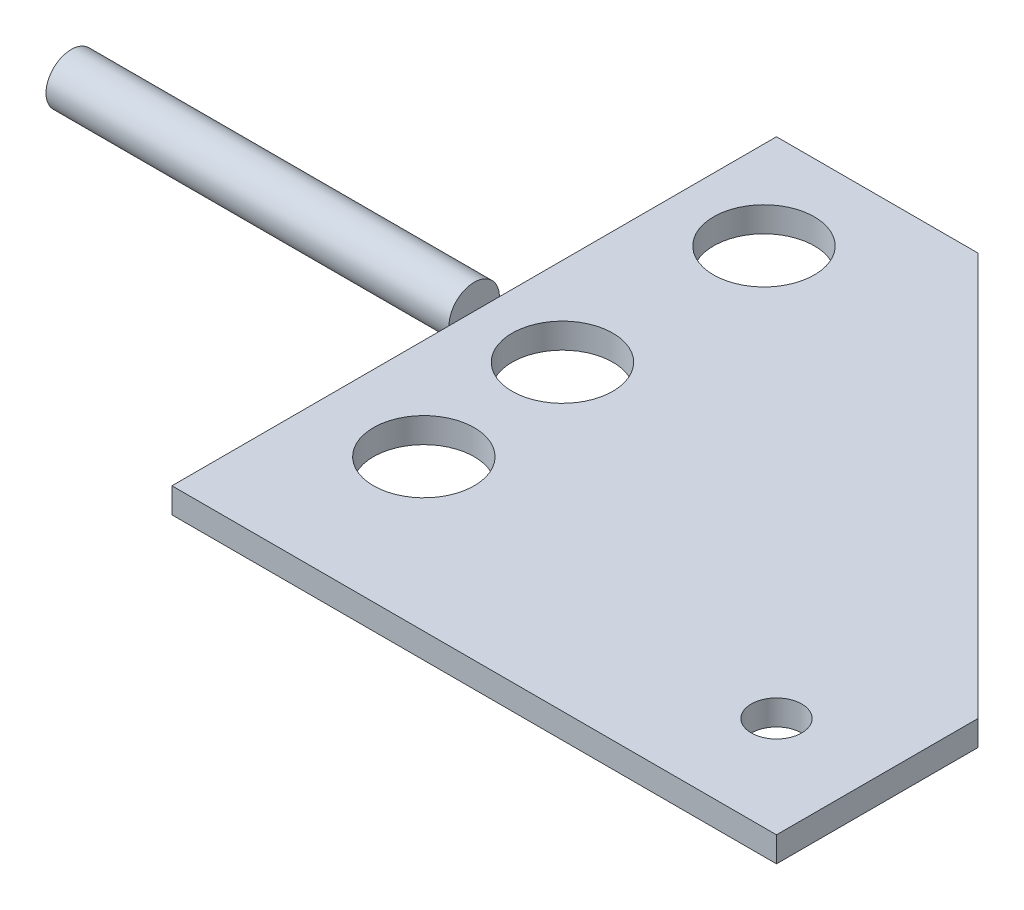
SolidWorks part; units mm, degrees
ref_plane "Front Plane" through (0, 0, 0) normal (0, 0, 1) x (1, 0, 0)
ref_plane "Top Plane" through (0, 0, 0) normal (0, 1, 0) x (1, 0, 0)
ref_plane "Right Plane" through (0, 0, 0) normal (1, 0, 0) x (0, 0, -1)
sketch "Sketch1" plane through (0, 0, 0) normal (0, 1, 0) x (1, 0, 0)
  line L0 (-76.2, 76.2) -> (-76.2, -76.2)
  line L1 (76.2, -76.2) -> (-76.2, -76.2) construction
  line L2 (76.2, -76.2) -> (76.2, 76.2) construction
  line L3 (76.2, 76.2) -> (-76.2, 76.2) construction
  line L4 (-76.2, -76.2) -> (-76.2, 76.2) construction
  line L5 (76.2, -76.2) -> (-76.2, 76.2) construction
  line L6 (76.2, 76.2) -> (-76.2, -76.2) construction
  line L7 (-76.2, -76.2) -> (76.2, -76.2)
  line L8 (76.2, -76.2) -> (76.2, -25.4)
  line L9 (76.2, -25.4) -> (-25.4, 76.2)
  line L10 (-25.4, 76.2) -> (-76.2, 76.2)
  point P0 (0, 0)
  dimension "D1" = 152.4
  dimension "D2" = 152.4
  dimension "D3" = 50.8
extrude "Boss-Extrude1" add sketch "Sketch1" along normal blind 6.35
sketch "Sketch2" plane through (-76.2, 0, 0) normal (-1, 0, 0) x (0, 0, 1)
  line L0 (-76.2, 6.35) -> (76.2, 6.35) construction
  circle A0 centre (0, 6.35) radius 6.35
  dimension "D1" = 12.7
extrude "Boss-Extrude2" add sketch "Sketch2" along normal blind 101.6
sketch "Sketch3" plane through (0, 6.35, 0) normal (0, 1, 0) x (1, 0, 0)
  line L1 (-76.2, -76.2) -> (-50.8, -76.2) construction
  line L2 (-76.2, -76.2) -> (-76.2, -38.1) construction
  line L3 (-76.2, -38.1) -> (-50.8, -38.1) construction
  line L4 (-50.8, -76.2) -> (-50.8, -38.1) construction
  line L5 (-76.2, -76.2) -> (-50.8, -38.1) construction
  line L6 (-76.2, -38.1) -> (-50.8, -76.2) construction
  line L7 (76.2, -76.2) -> (50.8, -76.2) construction
  line L8 (76.2, -76.2) -> (76.2, -50.8) construction
  line L9 (76.2, -50.8) -> (50.8, -50.8) construction
  line L10 (50.8, -76.2) -> (50.8, -50.8) construction
  line L11 (76.2, -76.2) -> (50.8, -50.8) construction
  line L12 (76.2, -50.8) -> (50.8, -76.2) construction
  circle A0 centre (-50.8, -38.1) radius 12.7
  circle A1 centre (50.8, -50.8) radius 6.35
  point P4 (-63.5, -57.15)
  point P11 (63.5, -63.5)
  dimension "D3" = 25.4
  dimension "D6" = 12.7
  dimension "D1" = 38.1
  dimension "D2" = 25.4
  dimension "D4" = 25.4
  dimension "D5" = 25.4
extrude "Cut-Extrude1" cut sketch "Sketch3" against normal blind 101.6
sketch "Sketch4" plane through (0, 6.35, 0) normal (0, 1, 0) x (1, 0, 0)
  line L0 (0, 0) -> (-53.9562, 0) construction
  circle A0 centre (-53.9562, 0) radius 12.7
  dimension "D1" = 25.4
extrude "Cut-Extrude2" cut sketch "Sketch4" against normal through all
sketch "Sketch5" plane through (0, 6.35, 0) normal (0, 1, 0) x (1, 0, 0)
  line L0 (-53.9562, 0) -> (-53.9562, 50.8) construction
  circle A0 centre (-53.9562, 50.8) radius 12.7
  dimension "D2" = 25.4
  dimension "D1" = 50.8
extrude "Cut-Extrude3" cut sketch "Sketch5" against normal through all both and the other way through all
